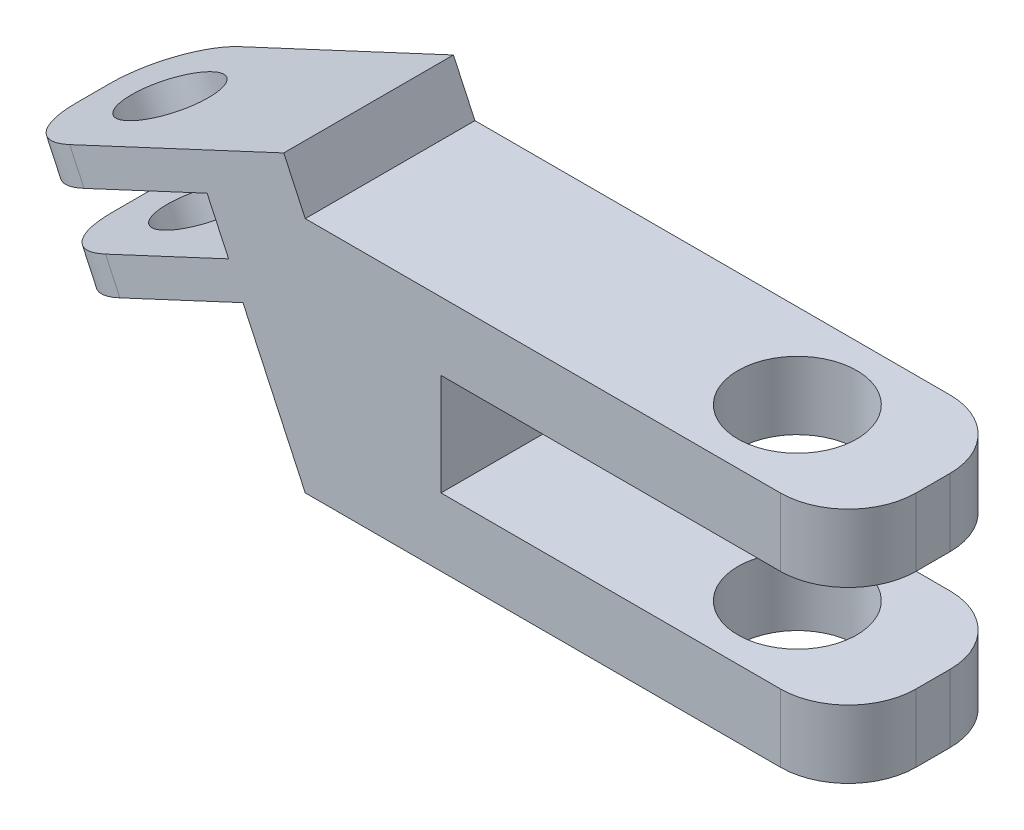
SolidWorks part; units mm, degrees
ref_plane "Front Plane" through (0, 0, 0) normal (0, 0, 1) x (1, 0, 0)
ref_plane "Top Plane" through (0, 0, 0) normal (0, 1, 0) x (1, 0, 0)
ref_plane "Right Plane" through (0, 0, 0) normal (1, 0, 0) x (0, 0, -1)
sketch "Sketch1" plane through (0, 0, 0) normal (0, 0, 1) x (1, 0, 0)
  line L0 (-8.7529, 1.0735) -> (-8.3303, 0.1672)
  line L1 (-7.6964, -1.1923) -> (-7.2738, -2.0986)
  line L2 (16, 3.5) -> (16, 1.5)
  line L3 (16, -1.5) -> (4, -1.5)
  line L4 (-8.3303, 0.1672) -> (-2.8925, 2.7029)
  line L5 (-2.8925, 2.7029) -> (-2.2585, 1.3434)
  line L6 (-2.2585, 1.3434) -> (-7.6964, -1.1923)
  line L7 (4, -1.5) -> (4, 1.5)
  line L8 (4, 1.5) -> (16, 1.5)
  line L9 (-7.2738, -2.0986) -> (-1.8359, 0.4371)
  line L10 (-1.8359, 0.4371) -> (0, -3.5)
  line L11 (0, -3.5) -> (16, -3.5)
  line L12 (-7.2738, -2.0986) -> (-7.6964, -1.1923)
  line L13 (-7.6964, -1.1923) -> (-2.2585, 1.3434)
  line L14 (-2.8925, 2.7029) -> (-8.3303, 0.1672)
  line L15 (-8.7529, 1.0735) -> (-0.6339, 4.8595)
  line L16 (-0.6339, 4.8595) -> (0, 3.5)
  line L17 (0, 3.5) -> (16, 3.5)
  line L18 (16, -1.5) -> (16, -3.5)
  point P18 (4, 0)
  dimension "D1" = 1.5
  dimension "D2" = 115
  dimension "D3" = 6
  dimension "D4" = 2
  dimension "D5" = 1
  dimension "D6" = 1
  dimension "D7" = 3
  dimension "D8" = 12
  dimension "D9" = 4
  dimension "D10" = 1.5
extrude "Boss-Extrude1" add sketch "Sketch1" along normal mid plane 5 contours L18 L3 L7 L8 L2 L17 L16 L15 L0 L4 L5 L6 L1 L9 L10 L11
sketch "Sketch2" plane through (-0.4953, 1.0623, 0) normal (0.4226, -0.9063, 0) x (0.9063, 0.4226, 0)
  line L1 (-7.4792, 2.5) -> (-7.4792, -2.5) construction
  circle A0 centre (-4.9792, 0) radius 1.25
  dimension "D1" = 2.5
  dimension "D2" = 2.5
extrude "Cut-Extrude1" cut sketch "Sketch2" against normal through all
sketch "Sketch3" plane through (0, 3.5, 0) normal (0, 1, 0) x (1, 0, 0)
  line L0 (16, -2.5) -> (16, 2.5) construction
  circle A0 centre (12, 0) radius 1.75
  dimension "D1" = 3.5
  dimension "D2" = 4
extrude "Cut-Extrude2" cut sketch "Sketch3" against normal through all
fillet "Fillet1" radius 2 8 edges at (16, -2.5, 2.5) (16, -2.5, -2.5) (16, 2.5, -2.5) (16, 2.5, 2.5) (-7.4851, -1.6454, -2.5) (-7.4851, -1.6454, 2.5) (-8.5416, 0.6204, -2.5) (-8.5416, 0.6204, 2.5)
